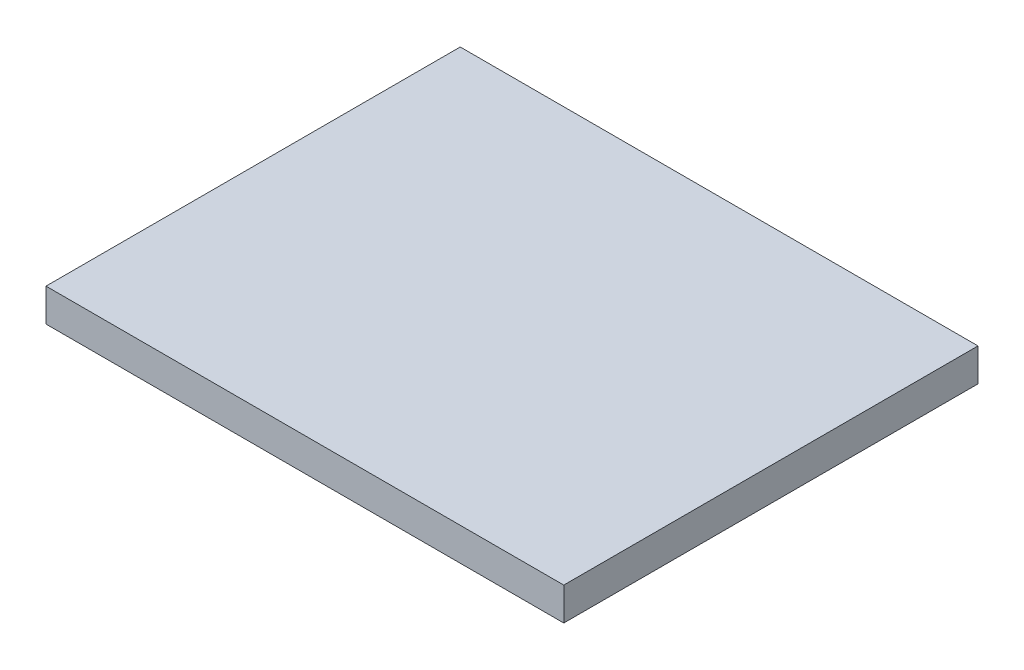
SolidWorks part; units mm, degrees
ref_plane "Front Plane" through (0, 0, 0) normal (0, 0, 1) x (1, 0, 0)
ref_plane "Top Plane" through (0, 0, 0) normal (0, 1, 0) x (1, 0, 0)
ref_plane "Right Plane" through (0, 0, 0) normal (1, 0, 0) x (0, 0, -1)
sketch "Sketch1" plane through (0, 0, 0) normal (0, 1, 0) x (1, 0, 0)
  line L1 (0, 0) -> (100, 0)
  line L2 (0, 0) -> (0, 80)
  line L3 (0, 80) -> (100, 80)
  line L4 (100, 0) -> (100, 80)
  dimension "D1" = 80
  dimension "D2" = 100
extrude "Boss-Extrude1" add sketch "Sketch1" along normal blind 6.35
